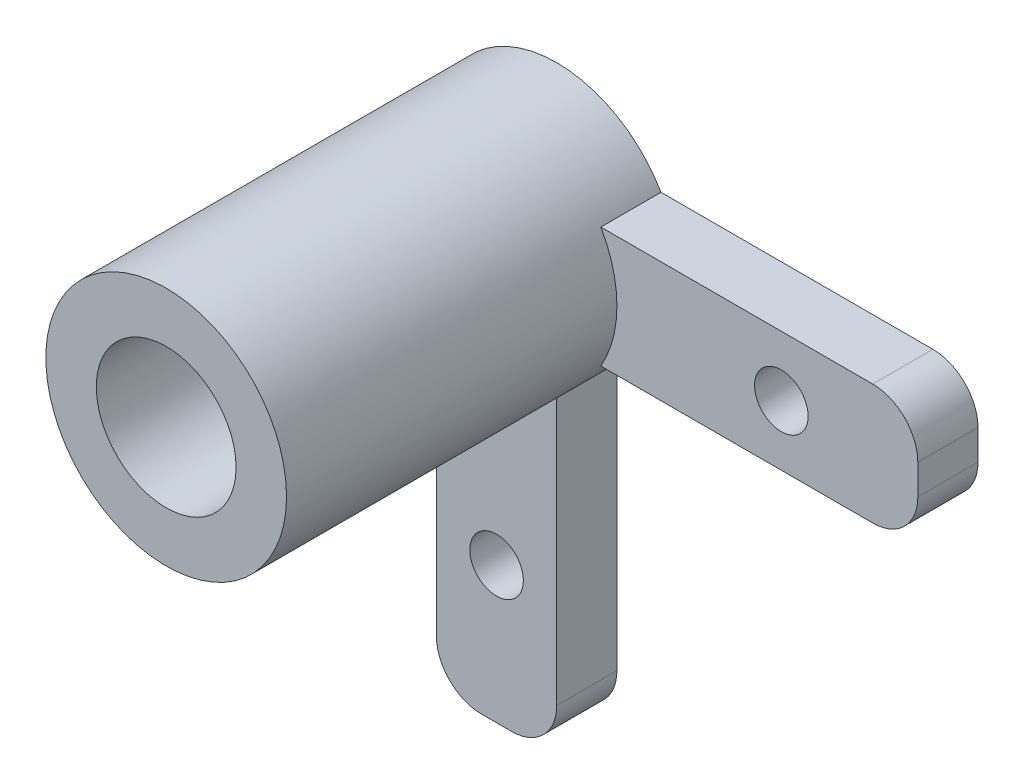
SolidWorks part; units mm, degrees
ref_plane "Front Plane" through (0, 0, 0) normal (0, 0, 1) x (1, 0, 0)
ref_plane "Top Plane" through (0, 0, 0) normal (0, 1, 0) x (1, 0, 0)
ref_plane "Right Plane" through (0, 0, 0) normal (1, 0, 0) x (0, 0, -1)
sketch "Sketch4" plane through (0, 0, 0) normal (0, 0, 1) x (1, 0, 0)
  line L0 (-30.1116, 27.8406) -> (-51.7016, 27.8406)
  line L1 (-51.7016, 22.7606) -> (-50.4316, 22.7606)
  line L2 (-45.3516, 22.7606) -> (-45.3516, 7.5206)
  line L3 (-30.1116, 22.7606) -> (-45.3516, 22.7606)
  line L4 (-30.1116, 22.7606) -> (-30.1116, 27.8406)
  line L5 (-45.3516, 7.5206) -> (-50.4316, 7.5206)
  line L6 (-50.4316, 7.5206) -> (-50.4316, 22.7606)
  line L10 (-51.7016, 27.8406) -> (-51.7016, 22.7606)
  point P0 (0, 0)
extrude "Extrude2" add sketch "Sketch4" along normal blind 2.54
sketch "Sketch8" plane through (0, 0, 2.54) normal (0, 0, 1) x (1, 0, 0)
  line L0 (-47.8916, 25.3006) -> (-35.8723, 25.3006) construction
  line L1 (-47.8916, 25.3006) -> (-47.8916, 13.2813) construction
  line L3 (-50.4316, 22.7606) -> (-45.3516, 22.7606) construction
  line L4 (-47.8916, 22.7606) -> (-47.8916, 27.8406) construction
  line L5 (-30.1116, 27.8406) -> (-51.7016, 27.8406) construction
  line L6 (-47.8916, 27.8406) -> (-47.8916, 25.3006) construction
sketch "Sketch5" plane through (0, 0, 2.54) normal (0, 0, 1) x (1, 0, 0)
  line L0 (-45.3516, 22.7606) -> (-50.4316, 22.7606) construction
  line L1 (-47.8916, 22.7606) -> (-47.8916, 27.8406) construction
  line L3 (-30.1116, 27.8406) -> (-51.7016, 27.8406) construction
  circle A0 centre (-47.8916, 25.3006) radius 5.08
extrude "Extrude3" add sketch "Sketch5" along normal blind 13.9446 and the other way blind 2.54
hole_wizard "#43 (0.089) Diameter Hole1" positions "3DSketch1" profile "Sketch9" hole size "#43" standard "Ansi Inch"
sketch3d "3DSketch1"
  point P0 (-47.8916, 13.2813, 2.54)
  point P3 (-35.8723, 25.3006, 2.54)
sketch "Sketch9" plane through (-47.8916, 13.2813, 2.54) normal (1, 0, 0) x (0, -1, 0)
  line L0 (0, 0) -> (0, 5.7592)
  line L1 (0, 5.7592) -> (1.1303, 5.08)
  line L2 (1.1303, 5.08) -> (1.1303, 0)
  line L5 (1.1303, 0) -> (0, 0)
  line L10 (0, 5.7592) -> (-1.1303, 5.08) construction
  line L11 (0, -6.35) -> (0, 107.95) construction
  dimension "Hole Dia." = 2.2606
  dimension "Hole Depth" = 5.08
  dimension "Drill Angle" = 118
sketch "Sketch11" plane through (0, 0, 16.4846) normal (0, 0, 1) x (1, 0, 0)
  circle A0 centre (-47.8916, 25.3006) radius 2.95
extrude "Extrude11" cut sketch "Sketch11" against normal through all
fillet "Fillet1" radius 1.905 4 edges at (-50.4316, 7.5206, 1.27) (-45.3516, 7.5206, 1.27) (-30.1116, 22.7606, 1.27) (-30.1116, 27.8406, 1.27)
